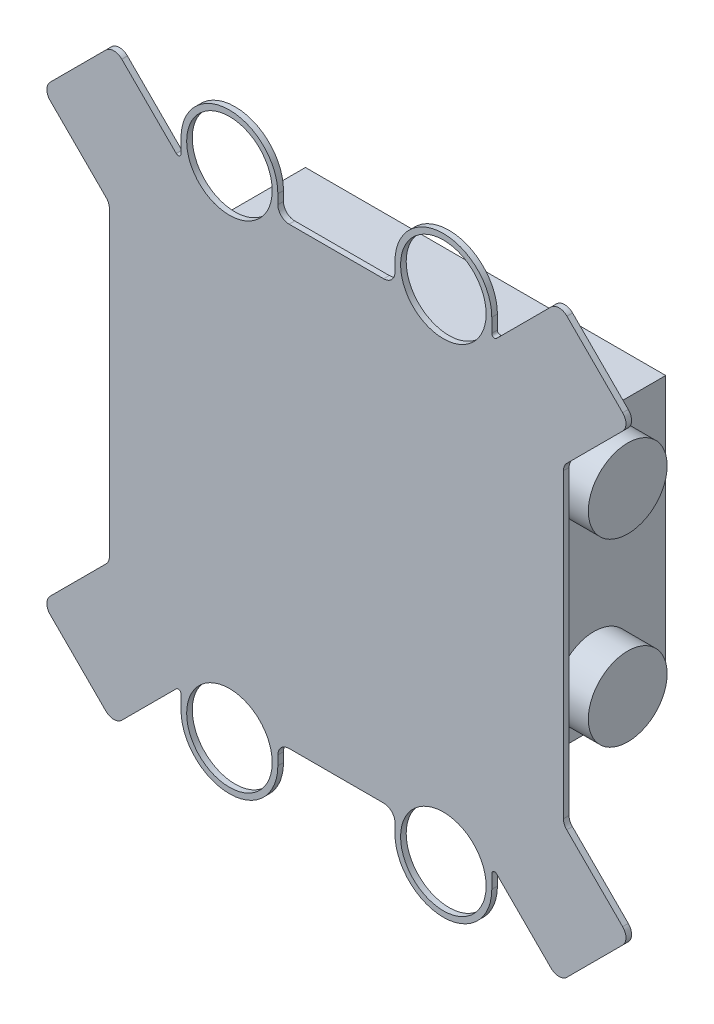
SolidWorks part; units mm, degrees
ref_plane "Front Plane" through (0, 0, 0) normal (0, 0, 1) x (1, 0, 0)
ref_plane "Top Plane" through (0, 0, 0) normal (0, 1, 0) x (1, 0, 0)
ref_plane "Right Plane" through (0, 0, 0) normal (1, 0, 0) x (0, 0, -1)
sketch "Sketch1" plane through (0, 0, 0) normal (0, 0, 1) x (1, 0, 0)
  line L48 (256.0823, -169.9995) -> (256.0823, 169.9995)
  line L49 (259.802, 178.9797) -> (322.8882, 242.0658)
  line L50 (322.8882, 260.0264) -> (260.0264, 322.8882)
  line L51 (242.0658, 322.8882) -> (180.6801, 261.5024)
  line L52 (175.26, 263.7474) -> (175.26, 279.4)
  line L53 (66.04, 279.4) -> (66.04, 268.7823)
  line L54 (53.34, 256.0823) -> (-53.34, 256.0823)
  line L55 (-66.04, 268.7823) -> (-66.04, 279.4)
  line L56 (-175.26, 279.4) -> (-175.26, 263.7474)
  line L57 (-180.6801, 261.5024) -> (-242.0658, 322.8882)
  line L58 (-260.0264, 322.8882) -> (-322.8882, 260.0264)
  line L59 (-322.8882, 242.0658) -> (-259.802, 178.9797)
  line L60 (-256.0823, 169.9995) -> (-256.0823, -169.9995)
  line L61 (-259.802, -178.9797) -> (-322.8882, -242.0658)
  line L62 (-322.8882, -260.0264) -> (-260.0264, -322.8882)
  line L63 (-242.0658, -322.8882) -> (-180.6801, -261.5024)
  line L64 (-175.26, -263.7474) -> (-175.26, -279.4)
  line L65 (-66.04, -279.4) -> (-66.04, -268.7823)
  line L66 (-53.34, -256.0823) -> (53.34, -256.0823)
  line L67 (66.04, -268.7823) -> (66.04, -279.4)
  line L68 (175.26, -279.4) -> (175.26, -263.7474)
  line L69 (180.6801, -261.5024) -> (242.0658, -322.8882)
  line L70 (260.0264, -322.8882) -> (322.8882, -260.0264)
  line L71 (322.8882, -242.0658) -> (259.802, -178.9797)
  arc A48 (256.0823, -169.9995) -> (259.802, -178.9797) centre (268.7823, -169.9995) ccw
  arc A49 (259.802, 178.9797) -> (256.0823, 169.9995) centre (268.7823, 169.9995) ccw
  arc A50 (322.8882, 242.0658) -> (322.8882, 260.0264) centre (313.9079, 251.0461) ccw
  arc A51 (260.0264, 322.8882) -> (242.0658, 322.8882) centre (251.0461, 313.9079) ccw
  arc A52 (175.26, 263.7474) -> (180.6801, 261.5024) centre (178.435, 263.7474) ccw
  arc A53 (175.26, 279.4) -> (66.04, 279.4) centre (120.65, 279.4) ccw
  arc A54 (53.34, 256.0823) -> (66.04, 268.7823) centre (53.34, 268.7823) ccw
  arc A55 (-66.04, 268.7823) -> (-53.34, 256.0823) centre (-53.34, 268.7823) ccw
  arc A56 (-66.04, 279.4) -> (-175.26, 279.4) centre (-120.65, 279.4) ccw
  arc A57 (-180.6801, 261.5024) -> (-175.26, 263.7474) centre (-178.435, 263.7474) ccw
  arc A58 (-242.0658, 322.8882) -> (-260.0264, 322.8882) centre (-251.0461, 313.9079) ccw
  arc A59 (-322.8882, 260.0264) -> (-322.8882, 242.0658) centre (-313.9079, 251.0461) ccw
  arc A60 (-256.0823, 169.9995) -> (-259.802, 178.9797) centre (-268.7823, 169.9995) ccw
  arc A61 (-259.802, -178.9797) -> (-256.0823, -169.9995) centre (-268.7823, -169.9995) ccw
  arc A62 (-322.8882, -242.0658) -> (-322.8882, -260.0264) centre (-313.9079, -251.0461) ccw
  arc A63 (-260.0264, -322.8882) -> (-242.0658, -322.8882) centre (-251.0461, -313.9079) ccw
  arc A64 (-175.26, -263.7474) -> (-180.6801, -261.5024) centre (-178.435, -263.7474) ccw
  arc A65 (-175.26, -279.4) -> (-66.04, -279.4) centre (-120.65, -279.4) ccw
  arc A66 (-53.34, -256.0823) -> (-66.04, -268.7823) centre (-53.34, -268.7823) ccw
  arc A67 (66.04, -268.7823) -> (53.34, -256.0823) centre (53.34, -268.7823) ccw
  arc A68 (66.04, -279.4) -> (175.26, -279.4) centre (120.65, -279.4) ccw
  arc A69 (180.6801, -261.5024) -> (175.26, -263.7474) centre (178.435, -263.7474) ccw
  arc A70 (242.0658, -322.8882) -> (260.0264, -322.8882) centre (251.0461, -313.9079) ccw
  arc A71 (322.8882, -260.0264) -> (322.8882, -242.0658) centre (313.9079, -251.0461) ccw
extrude "Boss-Extrude1" add sketch "Sketch1" along normal blind 6.35
sketch "Sketch2" plane through (0, 0, 0) normal (0, 0, -1) x (-1, 0, 0)
  line L1 (-203.2, -152.4) -> (203.2, -152.4)
  line L2 (-203.2, -152.4) -> (-203.2, 152.4)
  line L3 (-203.2, 152.4) -> (203.2, 152.4)
  line L4 (203.2, -152.4) -> (203.2, 152.4)
  line L5 (-203.2, -152.4) -> (203.2, 152.4) construction
  line L6 (-203.2, 152.4) -> (203.2, -152.4) construction
  point P0 (0, 0)
  dimension "D1" = 406.4
  dimension "D2" = 304.8
extrude "Boss-Extrude2" add sketch "Sketch2" along normal blind 161.925
sketch "Sketch3" plane through (0, 0, 0) normal (0, 0, -1) x (-1, 0, 0)
  arc A0 (-175.26, -279.4) -> (-66.04, -279.4) centre (-120.65, -279.4) ccw construction
  arc A1 (66.04, -279.4) -> (175.26, -279.4) centre (120.65, -279.4) ccw construction
  arc A2 (-175.26, -279.4) -> (-66.04, -279.4) centre (-120.65, -279.4) ccw
  arc A3 (66.04, -279.4) -> (175.26, -279.4) centre (120.65, -279.4) ccw
  arc A4 (175.26, 279.4) -> (66.04, 279.4) centre (120.65, 279.4) ccw construction
  arc A5 (-66.04, 279.4) -> (-175.26, 279.4) centre (-120.65, 279.4) ccw construction
  arc A6 (175.26, 279.4) -> (66.04, 279.4) centre (120.65, 279.4) ccw
  arc A7 (-66.04, 279.4) -> (-175.26, 279.4) centre (-120.65, 279.4) ccw
  circle A8 centre (-120.65, 279.4) radius 48.26
  circle A9 centre (120.65, 279.4) radius 48.26
  circle A10 centre (120.65, -279.4) radius 48.26
  circle A11 centre (-120.65, -279.4) radius 48.26
  dimension "D1" = 96.52
extrude "Cut-Extrude1" cut sketch "Sketch3" against normal blind 161.925 contours A9 | A8 | A11 | A10
sketch "Sketch4" plane through (203.2, 0, 0) normal (1, 0, 0) x (0, 0, -1)
  line L0 (80.9625, 152.4) -> (80.9625, -152.4) construction
  line L1 (161.925, 152.4) -> (0, 152.4) construction
  line L2 (161.925, -152.4) -> (0, -152.4) construction
  line L3 (161.925, 0) -> (0, 0) construction
  line L4 (161.925, 152.4) -> (161.925, -152.4) construction
  circle A0 centre (80.9625, 101.6) radius 44.45
  circle A1 centre (80.9625, -101.6) radius 44.45
  dimension "D1" = 88.9
  dimension "D2" = 88.9
  dimension "D3" = 101.6
  dimension "D4" = 101.6
extrude "Boss-Extrude3" add sketch "Sketch4" along normal blind 38.1
